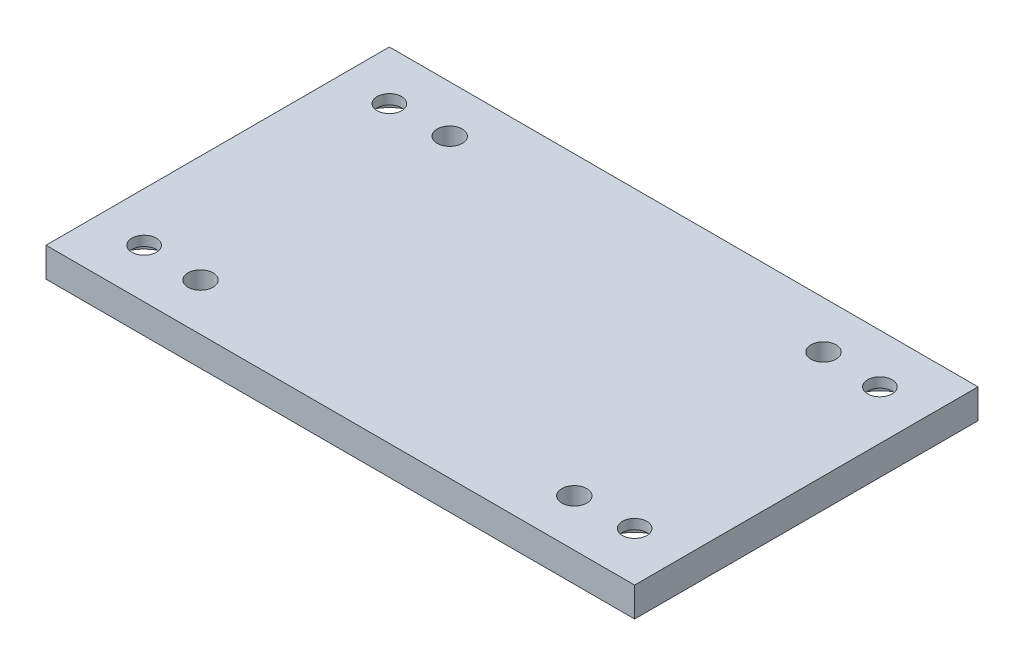
SolidWorks part; units mm, degrees
ref_plane "Front Plane" through (0, 0, 0) normal (0, 0, 1) x (1, 0, 0)
ref_plane "Top Plane" through (0, 0, 0) normal (0, 1, 0) x (1, 0, 0)
ref_plane "Right Plane" through (0, 0, 0) normal (1, 0, 0) x (0, 0, -1)
sketch "Sketch1" plane through (0, 0, 0) normal (0, 1, 0) x (1, 0, 0)
  line L0 (-55, 0) -> (55, 0) construction
  line L1 (-60, 35) -> (60, 35)
  line L2 (-60, 35) -> (-60, -35)
  line L3 (-60, -35) -> (60, -35)
  line L4 (60, 35) -> (60, -35)
  line L5 (-60, 35) -> (60, -35) construction
  line L6 (-60, -35) -> (60, 35) construction
  line L7 (0, -55) -> (0, 55) construction
  circle A0 centre (-50, -25) radius 2.5
  circle A1 centre (-50, 25) radius 2.5
  circle A2 centre (50, 25) radius 2.5
  circle A3 centre (50, -25) radius 2.5
  circle A4 centre (-63.5, 25.4) radius 2.5 construction
  circle A5 centre (-63.5, -25.4) radius 2.5 construction
  circle A6 centre (63.5, -25.4) radius 2.5 construction
  circle A7 centre (63.5, 25.4) radius 2.5 construction
  point P0 (0, 0)
  dimension "D3" = 5
  dimension "D1" = 70
  dimension "D2" = 120
  dimension "D4" = 25
  dimension "D5" = 50
  dimension "D6" = 25.4
  dimension "D7" = 63.5
extrude "Boss-Extrude1" add sketch "Sketch1" along normal blind 6
sketch "Sketch2" plane through (0, 6, 0) normal (0, 1, 0) x (1, 0, 0)
  line L0 (-55, 0) -> (55, 0) construction
  line L1 (0, -55) -> (0, 55) construction
  line L2 (-60, 35) -> (-60, -35) construction
  line L3 (-60, 0) -> (60, 0) construction
  line L4 (60, -35) -> (60, 35) construction
  line L5 (-38.1, -25.4) -> (38.1, -25.4) construction
  circle A0 centre (-50, 25) radius 5
  circle A1 centre (-50, -25) radius 5
  circle A2 centre (50, -25) radius 5
  circle A3 centre (50, 25) radius 5
  circle A8 centre (38.1, -25.4) radius 2.555
  circle A9 centre (-38.1, -25.4) radius 2.555
  circle A10 centre (38.1, 25.4) radius 2.555
  circle A11 centre (-38.1, 25.4) radius 2.555
  point P23 (0, -25.4)
  dimension "D1" = 10
  dimension "D5" = 5.11
  dimension "D2" = 5.11
  dimension "D4" = 76.2
  dimension "D6" = 25.4
  dimension "D7" = 50.8
extrude "Cut-Extrude1" cut sketch "Sketch2" against normal through all contours A9 | A11 | A8 | A10
sketch "Sketch3" plane through (0, 0, 0) normal (0, 1, 0) x (1, 0, 0)
  line L0 (0, -55) -> (0, 55) construction
  line L1 (-55, 0) -> (55, 0) construction
  circle A0 centre (-50, 25) radius 7.5
  circle A1 centre (50, 25) radius 7.5
  circle A2 centre (50, -25) radius 7.5
  circle A3 centre (-50, -25) radius 7.5
  dimension "D1" = 15
extrude "Cut-Extrude2" cut sketch "Sketch3" along normal blind 4
